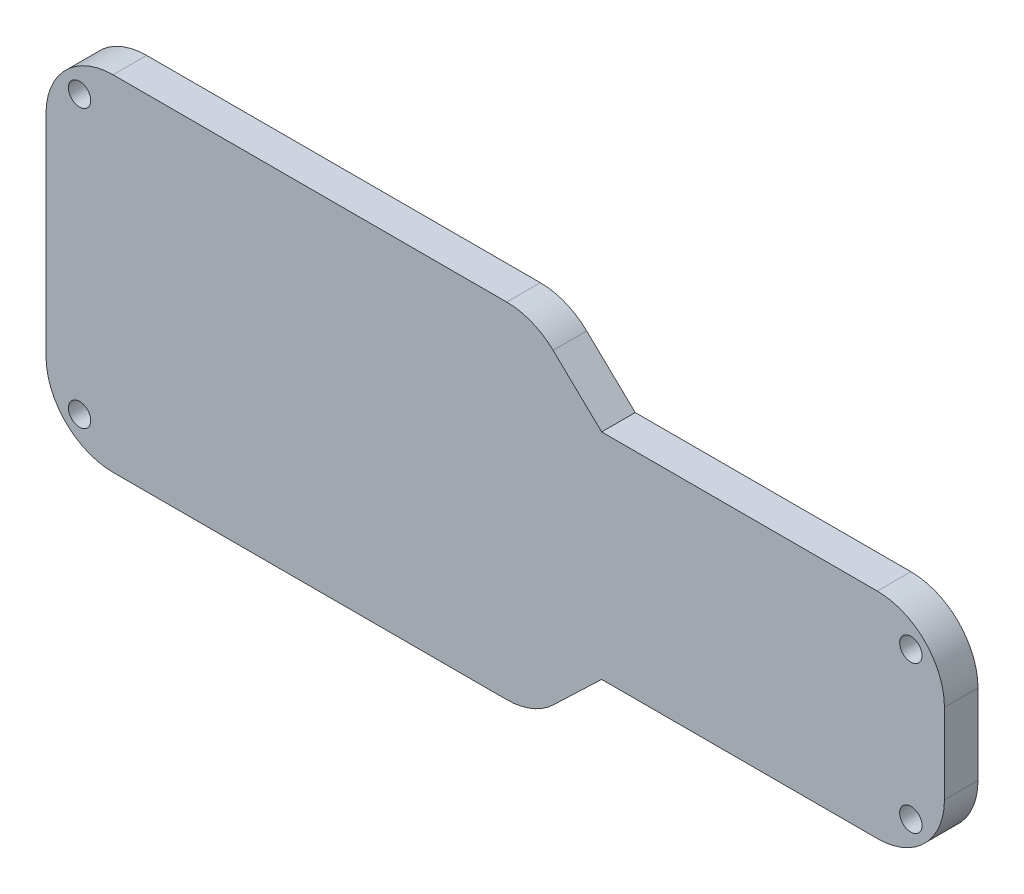
SolidWorks part; units mm, degrees
ref_plane "Front Plane" through (0, 0, 0) normal (0, 0, 1) x (1, 0, 0)
ref_plane "Top Plane" through (0, 0, 0) normal (0, 1, 0) x (1, 0, 0)
ref_plane "Right Plane" through (0, 0, 0) normal (1, 0, 0) x (0, 0, -1)
sketch "Sketch2" plane through (0, 0, 0) normal (0, 0, 1) x (1, 0, 0)
  line L0 (-34.29, 10.16) -> (0, 10.16)
  line L1 (-34.29, 10.16) -> (-34.29, 0)
  line L2 (-34.29, 0) -> (0, 0)
  line L3 (0, 10.16) -> (0, 0)
  line L4 (-69.31, 13.97) -> (-36.29, 13.97)
  line L5 (-69.31, 13.97) -> (-69.31, -3.81)
  line L6 (-69.31, -3.81) -> (-36.29, -3.81)
  line L7 (-36.29, 13.97) -> (-36.29, -3.81)
  line L8 (-31.29, 10.16) -> (-31.29, 0)
  line L9 (-71.31, 15.97) -> (-34.29, 15.97)
  line L10 (-34.29, 15.97) -> (-34.29, 12.16)
  line L11 (-34.29, 12.16) -> (-31.29, 12.16)
  line L12 (-31.29, 12.16) -> (-31.29, -2)
  line L13 (-31.29, -2) -> (-34.29, -2)
  line L14 (-34.29, -2) -> (-34.29, -5.81)
  line L15 (-34.29, -5.81) -> (-71.31, -5.81)
  line L16 (-71.31, -5.81) -> (-71.31, 15.97)
  point P4 (-34.29, 5.08)
  point P5 (-36.29, 5.08)
  dimension "D1" = 2
  dimension "D2" = 2
  dimension "D3" = 2
  dimension "D5" = 2
  dimension "D4" = 2
  dimension "D6" = 0
sketch "Sketch3" plane through (0, 0, 0) normal (0, 0, 1) x (1, 0, 0)
  line L0 (-69.81, 17.47) -> (-34.6251, 17.47)
  line L1 (-32.5518, 16.6383) -> (-28.2152, 12.4917)
  line L2 (-26.1419, 11.66) -> (-1.5, 11.66)
  line L3 (1.5, 8.66) -> (1.5, 1.5)
  line L4 (-1.5, -1.5) -> (-26.1419, -1.5)
  line L5 (-28.2152, -2.3317) -> (-32.5518, -6.4783)
  line L6 (-34.6251, -7.31) -> (-69.81, -7.31)
  line L7 (-72.81, -4.31) -> (-72.81, 14.47)
  line L8 (-71.31, 15.97) -> (-34.29, 15.97) construction
  line L9 (-34.29, -5.81) -> (-71.31, -5.81) construction
  line L11 (-34.29, 0) -> (0, 0) construction
  line L12 (0, 10.16) -> (0, 0) construction
  line L13 (-71.31, -5.81) -> (-71.31, 15.97) construction
  line L14 (-69.81, 20.47) -> (-34.6251, 20.47)
  line L15 (-30.4785, 18.8066) -> (-26.1419, 14.66)
  line L16 (-26.1419, 14.66) -> (-1.5, 14.66)
  line L17 (4.5, 8.66) -> (4.5, 1.5)
  line L18 (-1.5, -4.5) -> (-26.1419, -4.5)
  line L19 (-26.1419, -4.5) -> (-30.4785, -8.6466)
  line L20 (-34.6251, -10.31) -> (-69.81, -10.31)
  line L21 (-75.81, -4.31) -> (-75.81, 14.47)
  arc A0 (-69.81, -7.31) -> (-72.81, -4.31) centre (-69.81, -4.31) cw
  arc A1 (-1.5, 11.66) -> (1.5, 8.66) centre (-1.5, 8.66) cw
  arc A2 (1.5, 1.5) -> (-1.5, -1.5) centre (-1.5, 1.5) cw
  arc A3 (-32.5518, -6.4783) -> (-34.6251, -7.31) centre (-34.6251, -4.31) cw
  arc A4 (-26.1419, -1.5) -> (-28.2152, -2.3317) centre (-26.1419, -4.5) ccw
  arc A5 (-28.2152, 12.4917) -> (-26.1419, 11.66) centre (-26.1419, 14.66) ccw
  arc A6 (-34.6251, 17.47) -> (-32.5518, 16.6383) centre (-34.6251, 14.47) cw
  arc A7 (-69.81, 17.47) -> (-72.81, 14.47) centre (-69.81, 14.47) ccw
  arc A8 (-34.6251, 20.47) -> (-30.4785, 18.8066) centre (-34.6251, 14.47) cw
  arc A9 (-26.1419, 14.66) -> (-26.1419, 14.66) centre (-26.1419, 14.66) ccw
  arc A10 (-1.5, 14.66) -> (4.5, 8.66) centre (-1.5, 8.66) cw
  arc A11 (4.5, 1.5) -> (-1.5, -4.5) centre (-1.5, 1.5) cw
  arc A12 (-26.1419, -4.5) -> (-26.1419, -4.5) centre (-26.1419, -4.5) ccw
  arc A13 (-30.4785, -8.6466) -> (-34.6251, -10.31) centre (-34.6251, -4.31) cw
  arc A14 (-69.81, -10.31) -> (-75.81, -4.31) centre (-69.81, -4.31) cw
  arc A15 (-69.81, 20.47) -> (-75.81, 14.47) centre (-69.81, 14.47) ccw
  circle A16 centre (-72.81, 17.47) radius 1
  circle A17 centre (-72.81, -7.31) radius 1
  circle A18 centre (1.5, -1.5) radius 1
  circle A19 centre (1.5, 11.66) radius 1
  point P26 (-33.4216, -7.31)
  point P29 (-27.3454, -1.5)
  point P32 (-27.3454, 11.66)
  point P35 (-33.4216, 17.47)
  dimension "D5" = 3
  dimension "D6" = 2
  dimension "D1" = 1.5
  dimension "D2" = 1.5
  dimension "D3" = 1.5
  dimension "D4" = 1.5
extrude "Boss-Extrude2" add sketch "Sketch3" along normal blind 3
sketch "Sketch5" [suppressed] plane through (0, 0, 0) normal (0, 0, -1) x (-1, 0, 0)
  line L0 (-1.5, 1.5) -> (-1.5, 8.66) construction
  line L1 (26.1419, -1.5) -> (1.5, -1.5) construction
  line L2 (32.5518, -6.4783) -> (28.2152, -2.3317) construction
  line L3 (69.81, -7.31) -> (34.6251, -7.31) construction
  line L4 (72.81, 14.47) -> (72.81, -4.31) construction
  line L5 (-1.5, 1.5) -> (-1.5, 8.66)
  line L6 (26.1419, -1.5) -> (1.5, -1.5)
  line L7 (32.5518, -6.4783) -> (28.2152, -2.3317)
  line L8 (72.81, -4.31) -> (72.81, 14.47)
  line L9 (34.6251, -7.31) -> (69.81, -7.31)
  line L10 (28.2152, -2.3317) -> (32.5518, -6.4783)
  line L11 (1.5, -1.5) -> (26.1419, -1.5)
  line L12 (-1.5, 8.66) -> (-1.5, 1.5)
  line L13 (26.1419, 11.66) -> (1.5, 11.66)
  line L14 (32.5518, 16.6383) -> (28.2152, 12.4917)
  line L15 (69.81, 17.47) -> (34.6251, 17.47)
  line L16 (72.81, -4.31) -> (72.81, 14.47)
  line L17 (34.6251, -7.31) -> (69.81, -7.31)
  line L18 (28.2152, -2.3317) -> (32.5518, -6.4783)
  line L19 (1.5, -1.5) -> (26.1419, -1.5)
  line L20 (-1.5, 8.66) -> (-1.5, 1.5)
  line L21 (26.1419, 11.66) -> (1.5, 11.66)
  line L22 (32.5518, 16.6383) -> (28.2152, 12.4917)
  line L23 (69.81, 17.47) -> (34.6251, 17.47)
  line L24 (69.81, -7.31) -> (34.6251, -7.31)
  line L25 (72.81, 14.47) -> (72.81, -4.31)
  arc A0 (1.5, 11.66) -> (-1.5, 8.66) centre (1.5, 8.66) ccw construction
  arc A1 (-1.5, 1.5) -> (1.5, -1.5) centre (1.5, 1.5) ccw construction
  arc A2 (28.2152, -2.3317) -> (26.1419, -1.5) centre (26.1419, -4.5) ccw construction
  arc A3 (32.5518, -6.4783) -> (34.6251, -7.31) centre (34.6251, -4.31) ccw construction
  arc A4 (69.81, -7.31) -> (72.81, -4.31) centre (69.81, -4.31) ccw construction
  arc A5 (72.81, 14.47) -> (69.81, 17.47) centre (69.81, 14.47) ccw construction
  arc A6 (1.5, 11.66) -> (-1.5, 8.66) centre (1.5, 8.66) ccw
  arc A7 (-1.5, 1.5) -> (1.5, -1.5) centre (1.5, 1.5) ccw
  arc A8 (69.81, -7.31) -> (72.81, -4.31) centre (69.81, -4.31) ccw
  arc A9 (32.5518, -6.4783) -> (34.6251, -7.31) centre (34.6251, -4.31) ccw
  arc A10 (28.2152, -2.3317) -> (26.1419, -1.5) centre (26.1419, -4.5) ccw
  arc A11 (-1.5, 1.5) -> (1.5, -1.5) centre (1.5, 1.5) ccw
  arc A12 (1.5, 11.66) -> (-1.5, 8.66) centre (1.5, 8.66) ccw
  arc A13 (26.1419, 11.66) -> (28.2152, 12.4917) centre (26.1419, 14.66) ccw
  arc A14 (34.6251, 17.47) -> (32.5518, 16.6383) centre (34.6251, 14.47) ccw
  arc A15 (72.81, 14.47) -> (69.81, 17.47) centre (69.81, 14.47) ccw
  arc A16 (69.81, -7.31) -> (72.81, -4.31) centre (69.81, -4.31) ccw
  arc A17 (32.5518, -6.4783) -> (34.6251, -7.31) centre (34.6251, -4.31) ccw
  arc A18 (28.2152, -2.3317) -> (26.1419, -1.5) centre (26.1419, -4.5) ccw
  arc A19 (-1.5, 1.5) -> (1.5, -1.5) centre (1.5, 1.5) ccw
  arc A20 (1.5, 11.66) -> (-1.5, 8.66) centre (1.5, 8.66) ccw
  arc A21 (26.1419, 11.66) -> (28.2152, 12.4917) centre (26.1419, 14.66) ccw
  arc A22 (34.6251, 17.47) -> (32.5518, 16.6383) centre (34.6251, 14.47) ccw
  arc A23 (72.81, 14.47) -> (69.81, 17.47) centre (69.81, 14.47) ccw
  arc A24 (28.2152, -2.3317) -> (26.1419, -1.5) centre (26.1419, -4.5) ccw
  arc A25 (32.5518, -6.4783) -> (34.6251, -7.31) centre (34.6251, -4.31) ccw
  arc A26 (69.81, -7.31) -> (72.81, -4.31) centre (69.81, -4.31) ccw
  arc A27 (72.81, 14.47) -> (69.81, 17.47) centre (69.81, 14.47) ccw
  dimension "D1" = 0
sketch "Sketch7" [suppressed] plane through (0, 0, 3) normal (0, 0, 1) x (1, 0, 0)
  circle A0 centre (-72.81, 17.47) radius 1 construction
  circle A1 centre (-72.81, 17.47) radius 1
  circle A2 centre (1.5, -1.5) radius 1 construction
  circle A3 centre (1.5, -1.5) radius 1
  circle A4 centre (1.5, 11.66) radius 1 construction
  circle A5 centre (1.5, 11.66) radius 1
  circle A6 centre (-72.81, -7.31) radius 1 construction
  circle A7 centre (-72.81, -7.31) radius 1
sketch "Sketch8" plane through (0, 0, 3) normal (0, 0, 1) x (1, 0, 0)
  line L0 (-72.81, 14.47) -> (-72.81, -4.31) construction
  line L1 (-34.6251, 17.47) -> (-69.81, 17.47) construction
  line L2 (-28.2152, 12.4917) -> (-32.5518, 16.6383) construction
  line L3 (-1.5, 11.66) -> (-26.1419, 11.66) construction
  line L4 (-26.1419, -1.5) -> (-1.5, -1.5) construction
  line L5 (1.5, 1.5) -> (1.5, 8.66) construction
  line L6 (-32.5518, -6.4783) -> (-28.2152, -2.3317) construction
  line L7 (-69.81, -7.31) -> (-34.6251, -7.31) construction
  line L8 (-72.81, 14.47) -> (-72.81, -4.31)
  line L9 (-34.6251, 17.47) -> (-69.81, 17.47)
  line L10 (-28.2152, 12.4917) -> (-32.5518, 16.6383)
  line L11 (-1.5, 11.66) -> (-26.1419, 11.66)
  line L12 (-26.1419, -1.5) -> (-1.5, -1.5)
  line L13 (1.5, 1.5) -> (1.5, 8.66)
  line L14 (-32.5518, -6.4783) -> (-28.2152, -2.3317)
  line L15 (-69.81, -7.31) -> (-34.6251, -7.31)
  arc A0 (-69.81, 17.47) -> (-72.81, 14.47) centre (-69.81, 14.47) ccw construction
  arc A1 (-32.5518, 16.6383) -> (-34.6251, 17.47) centre (-34.6251, 14.47) ccw construction
  arc A2 (-28.2152, 12.4917) -> (-26.1419, 11.66) centre (-26.1419, 14.66) ccw construction
  arc A3 (1.5, 8.66) -> (-1.5, 11.66) centre (-1.5, 8.66) ccw construction
  arc A4 (-1.5, -1.5) -> (1.5, 1.5) centre (-1.5, 1.5) ccw construction
  arc A5 (-26.1419, -1.5) -> (-28.2152, -2.3317) centre (-26.1419, -4.5) ccw construction
  arc A6 (-34.6251, -7.31) -> (-32.5518, -6.4783) centre (-34.6251, -4.31) ccw construction
  arc A7 (-72.81, -4.31) -> (-69.81, -7.31) centre (-69.81, -4.31) ccw construction
  arc A8 (-69.81, 17.47) -> (-72.81, 14.47) centre (-69.81, 14.47) ccw
  arc A9 (-32.5518, 16.6383) -> (-34.6251, 17.47) centre (-34.6251, 14.47) ccw
  arc A10 (-28.2152, 12.4917) -> (-26.1419, 11.66) centre (-26.1419, 14.66) ccw
  arc A11 (1.5, 8.66) -> (-1.5, 11.66) centre (-1.5, 8.66) ccw
  arc A12 (-1.5, -1.5) -> (1.5, 1.5) centre (-1.5, 1.5) ccw
  arc A13 (-26.1419, -1.5) -> (-28.2152, -2.3317) centre (-26.1419, -4.5) ccw
  arc A14 (-34.6251, -7.31) -> (-32.5518, -6.4783) centre (-34.6251, -4.31) ccw
  arc A15 (-72.81, -4.31) -> (-69.81, -7.31) centre (-69.81, -4.31) ccw
extrude "Boss-Extrude5" add sketch "Sketch8" against normal blind 3
equation "\"D5@Sketch2\"=\"pcb_overflow\""
equation "\"D1@Sketch2\"=\"pcb_overflow\""
equation "\"D2@Sketch2\"=\"pcb_overflow\""
equation "\"D4@Sketch2\"=\"pcb_overflow\""
equation "\"D3@Sketch2\"=\"pcb_overflow\""
equation "\"D1@Sketch3\"=\"gap_from_case\""
equation "\"D2@Sketch3\"=\"gap_from_case\""
equation "\"D3@Sketch3\"=\"gap_from_case\""
equation "\"D4@Sketch3\"=\"gap_from_case\""
equation "\"D6@Sketch3\"=\"notch_dia\""
